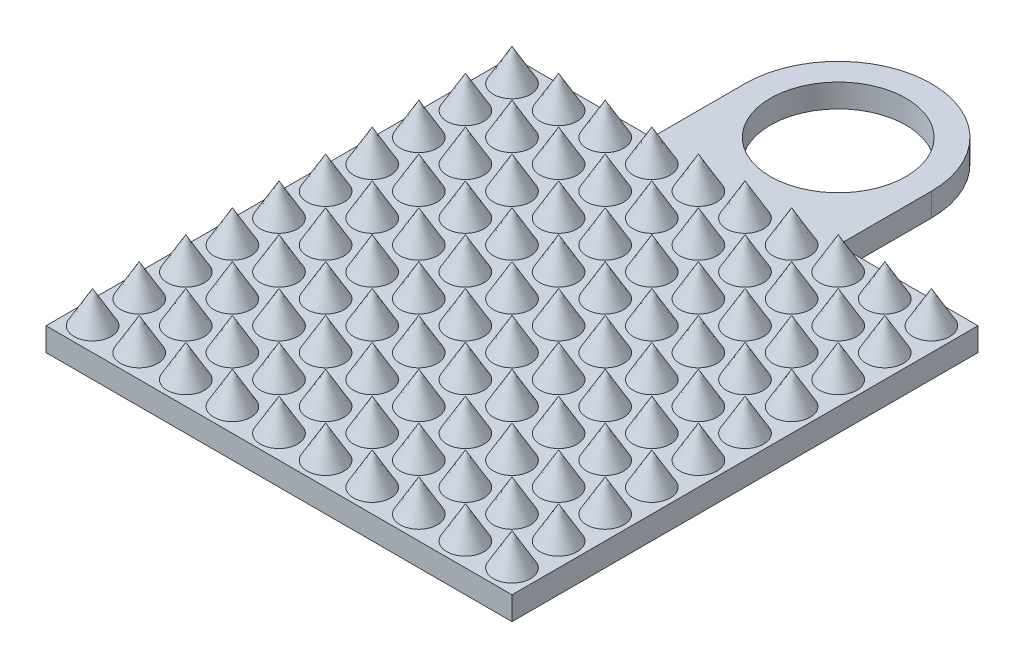
SolidWorks part; units mm, degrees
ref_plane "Front Plane" through (0, 0, 0) normal (0, 0, 1) x (1, 0, 0)
ref_plane "Top Plane" through (0, 0, 0) normal (0, 1, 0) x (1, 0, 0)
ref_plane "Right Plane" through (0, 0, 0) normal (1, 0, 0) x (0, 0, -1)
sketch "Sketch1" plane through (0, 0, 0) normal (0, 1, 0) x (1, 0, 0)
  line L1 (5, -5) -> (-5, -5)
  line L2 (5, -5) -> (5, 5)
  line L3 (5, 5) -> (-5, 5)
  line L4 (-5, -5) -> (-5, 5)
  line L5 (5, -5) -> (-5, 5) construction
  line L6 (5, 5) -> (-5, -5) construction
  point P0 (0, 0)
  dimension "D1" = 10
  dimension "D2" = 10
extrude "Plate" add sketch "Sketch1" along normal blind 0.5
sketch "Sketch2" plane through (0, 0.5, 0) normal (0, 1, 0) x (1, 0, 0)
  line L0 (-5, -5) -> (5, -5) construction
  line L1 (-5, 5) -> (-5, -5) construction
  circle A0 centre (-4.5, -4.5) radius 0.4
  dimension "D1" = 0.8
  dimension "D2" = 0.5
  dimension "D3" = 0.5
sketch "Sketch4" plane through (0, 0, 0) normal (0, 1, 0) x (1, 0, 0)
  line L5 (-2, 7) -> (-2, 5)
  line L6 (5, 5) -> (-5, 5) construction
  line L8 (-5, 5) -> (-5, -5) construction
  line L9 (-2, 5) -> (2, 5)
  line L10 (2, 5) -> (2, 7)
  arc A0 (-2, 7) -> (2, 7) centre (0, 7) cw
  point P0 (0, 7)
  dimension "D3" = 5
extrude "Boss-Extrude3" add sketch "Sketch4" along normal blind 0.5
sketch "Sketch5" plane through (0, 0.5, 0) normal (0, 1, 0) x (1, 0, 0)
  circle A0 centre (0, 7) radius 1.4559
extrude "Cut-Extrude1" cut sketch "Sketch5" against normal blind 1.5 and the other way blind 0.5
extrude "Boss-Extrude4" add sketch "Sketch2" along normal blind 10.25 draft 30
pattern_linear "LPattern1" count 10 spacing 1 along (1, 0, 0) count 10 spacing 1 along (0, 0, -1) of "Boss-Extrude4"
